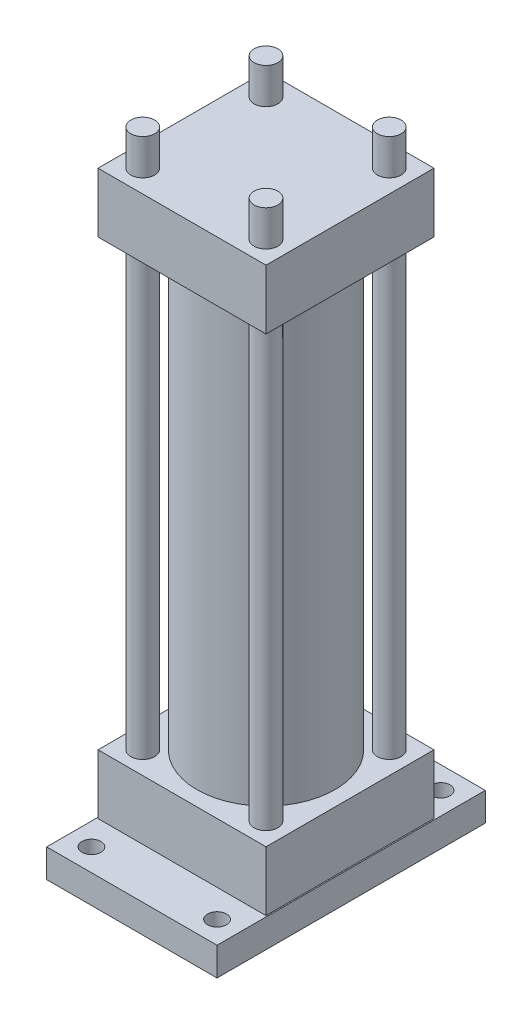
SolidWorks part; units mm, degrees
ref_plane "Alzado" through (0, 0, 0) normal (0, 0, 1) x (1, 0, 0)
ref_plane "Planta" through (0, 0, 0) normal (0, 1, 0) x (1, 0, 0)
ref_plane "Vista lateral" through (0, 0, 0) normal (1, 0, 0) x (0, 0, -1)
sketch "Croquis1" plane through (0, 0, 0) normal (0, 1, 0) x (1, 0, 0)
  line L1 (-57.15, -90) -> (57.15, -90)
  line L2 (-57.15, -90) -> (-57.15, 90)
  line L3 (-57.15, 90) -> (57.15, 90)
  line L4 (57.15, -90) -> (57.15, 90)
  line L5 (-57.15, -90) -> (57.15, 90) construction
  line L6 (-57.15, 90) -> (57.15, -90) construction
  point P0 (0, 0)
  dimension "D1" = 180
  dimension "D2" = 114.3
extrude "Saliente-Extruir1" add sketch "Croquis1" along normal blind 19.05
sketch "Croquis2" plane through (0, 19.05, 0) normal (0, 1, 0) x (1, 0, 0)
  line L0 (57.15, 90) -> (-57.15, 90) construction
  line L1 (-57.15, 90) -> (-57.15, -90) construction
  line L2 (0, 90) -> (0, -90) construction
  line L3 (-57.15, -90) -> (57.15, -90) construction
  line L4 (-57.15, 0) -> (57.15, 0) construction
  line L5 (57.15, -90) -> (57.15, 90) construction
  circle A0 centre (-42.15, 75) radius 6.35
  circle A1 centre (42.15, 75) radius 6.35
  circle A2 centre (42.15, -75) radius 6.35
  circle A3 centre (-42.15, -75) radius 6.35
  dimension "D1" = 12.7
  dimension "D3" = 15
  dimension "D2" = 15
extrude "Cortar-Extruir1" cut sketch "Croquis2" against normal blind 19.05
sketch "Croquis3" plane through (0, 19.05, 0) normal (0, 1, 0) x (1, 0, 0)
  line L0 (0, 90) -> (0, -90) construction
  line L1 (57.15, 90) -> (-57.15, 90) construction
  line L2 (-57.15, -90) -> (57.15, -90) construction
  line L4 (56.3563, -56.3562) -> (-56.3562, -56.3563)
  line L5 (56.3563, -56.3562) -> (56.3563, 56.3563)
  line L6 (56.3563, 56.3563) -> (-56.3562, 56.3562)
  line L7 (-56.3562, -56.3563) -> (-56.3562, 56.3562)
  line L8 (56.3563, -56.3562) -> (-56.3562, 56.3562) construction
  line L9 (56.3563, 56.3563) -> (-56.3562, -56.3563) construction
  point P6 (0, 0)
  dimension "D1" = 112.7125
  dimension "D2" = 112.7125
extrude "Saliente-Extruir2" add sketch "Croquis3" along normal blind 40
sketch "Croquis4" plane through (0, 59.05, 0) normal (0, 1, 0) x (1, 0, 0)
  line L0 (-56.3562, 56.3562) -> (-56.3562, -56.3563) construction
  line L1 (56.3563, 56.3563) -> (-56.3562, 56.3562) construction
  line L2 (0, 56.3562) -> (0, -56.3562) construction
  line L3 (56.3563, 56.3563) -> (-56.3562, 56.3562) construction
  line L4 (-56.3562, -56.3563) -> (56.3563, -56.3562) construction
  line L5 (-56.3562, 0) -> (56.3563, 0) construction
  line L6 (56.3563, -56.3562) -> (56.3563, 56.3563) construction
  circle A0 centre (-41.3562, 41.3563) radius 8
  circle A1 centre (41.3563, 41.3562) radius 8
  circle A2 centre (41.3562, -41.3563) radius 8
  circle A3 centre (-41.3562, -41.3562) radius 8
  dimension "D3" = 16
  dimension "D1" = 15
  dimension "D2" = 15
extrude "Cortar-Extruir2" cut sketch "Croquis4" against normal blind 40
sketch "Croquis5" plane through (0, 19.05, 0) normal (0, 1, 0) x (1, 0, 0)
  circle A0 centre (-41.3562, 41.3563) radius 8
  circle A1 centre (41.3563, 41.3562) radius 8
  circle A2 centre (41.3562, -41.3563) radius 8
  circle A3 centre (-41.3562, -41.3562) radius 8
extrude "Saliente-Extruir3" add sketch "Croquis5" along normal blind 338
sketch "Croquis6" plane through (0, 59.05, 0) normal (0, 1, 0) x (1, 0, 0)
  circle A0 centre (0, 0) radius 38.1
  dimension "D1" = 76.2
extrude "Cortar-Extruir3" cut sketch "Croquis6" against normal blind 10
sketch "Croquis7" plane through (0, 59.05, 0) normal (0, 1, 0) x (1, 0, 0)
  circle A0 centre (0, 0) radius 46.355
  dimension "D1" = 92.71
extrude "Saliente-Extruir4" add sketch "Croquis7" along normal blind 298
sketch "Croquis8" plane through (0, 357.05, 0) normal (0, 1, 0) x (1, 0, 0)
  line L0 (0, 56.3562) -> (0, -56.3562) construction
  line L1 (56.3563, 56.3563) -> (-56.3562, 56.3562) construction
  line L2 (-56.3562, -56.3563) -> (56.3563, -56.3562) construction
  line L4 (-56.3563, -56.3563) -> (56.3563, -56.3563)
  line L5 (-56.3563, -56.3563) -> (-56.3563, 56.3563)
  line L6 (-56.3563, 56.3563) -> (56.3563, 56.3563)
  line L7 (56.3563, -56.3563) -> (56.3563, 56.3563)
  line L8 (-56.3563, -56.3563) -> (56.3563, 56.3563) construction
  line L9 (-56.3563, 56.3563) -> (56.3563, -56.3563) construction
  point P6 (0, 0)
extrude "Saliente-Extruir5" add sketch "Croquis8" along normal blind 40
sketch "Croquis9" plane through (0, 397.05, 0) normal (0, 1, 0) x (1, 0, 0)
  circle A0 centre (-41.3562, 41.3563) radius 8
  circle A1 centre (41.3563, 41.3562) radius 8
  circle A2 centre (-41.3562, -41.3562) radius 8
  circle A3 centre (41.3562, -41.3563) radius 8
extrude "Saliente-Extruir6" add sketch "Croquis9" along normal blind 24
